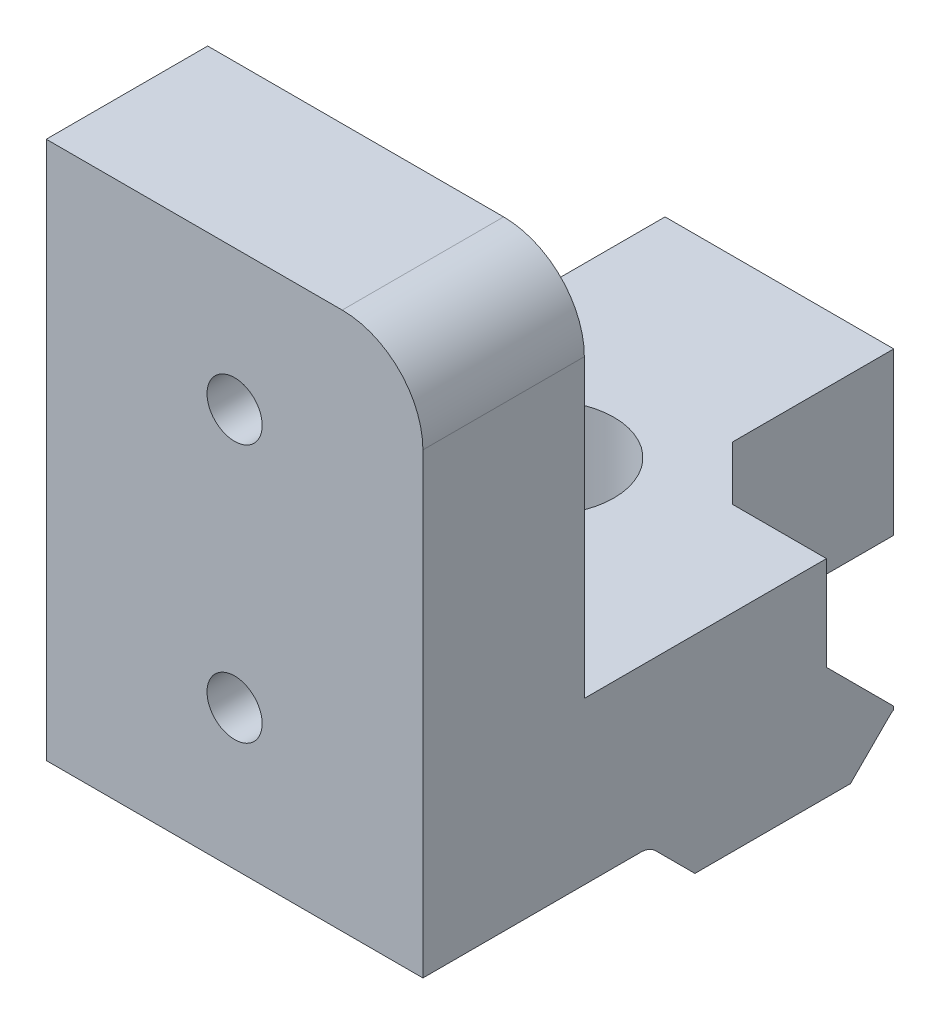
SolidWorks part; units mm, degrees
ref_plane "Front Plane" through (0, 0, 0) normal (0, 0, 1) x (1, 0, 0)
ref_plane "Top Plane" through (0, 0, 0) normal (0, 1, 0) x (1, 0, 0)
ref_plane "Right Plane" through (0, 0, 0) normal (1, 0, 0) x (0, 0, -1)
sketch "Sketch1" plane through (32.3643, 0, 0) normal (1, 0, 0) x (0, 0, -1)
  line L0 (-10.7659, 34.0751) -> (-4.9859, 34.0751)
  line L1 (-17.8759, 35.7651) -> (2.1241, 35.7651)
  line L2 (-17.8759, 35.7651) -> (-17.8759, 41.7651)
  line L3 (-17.8759, 41.7651) -> (2.1241, 41.7651)
  line L4 (2.1241, 35.7651) -> (2.1241, 41.7651)
  line L52 (-5.5365, 22.3651) -> (-2.3759, 19.2044)
  line L53 (-2.3759, 19.2044) -> (-2.3759, 17.5651)
  line L54 (-2.3759, 17.5651) -> (-4.9859, 17.5651)
  line L55 (-4.9859, 17.5651) -> (-4.9859, 17.4551)
  line L56 (-4.9859, 17.4551) -> (-3.5273, 15.9964)
  line L57 (-2.9686, 15.7651) -> (0.6241, 15.7651)
  line L58 (2.1241, 17.2651) -> (2.1241, 20.8578)
  line L59 (1.8927, 21.4164) -> (0.4341, 22.8751)
  line L60 (0.4341, 22.8751) -> (0.3241, 22.8751)
  line L61 (0.3241, 22.8751) -> (0.3241, 20.2651)
  line L62 (0.3241, 20.2651) -> (-1.3152, 20.2651)
  line L63 (-1.3152, 20.2651) -> (-4.4759, 23.4257)
  line L64 (-4.4759, 23.4257) -> (-4.4759, 28.1044)
  line L65 (-4.4759, 28.1044) -> (-1.3152, 31.2651)
  line L66 (-1.3152, 31.2651) -> (0.3241, 31.2651)
  line L67 (0.3241, 31.2651) -> (0.3241, 28.6551)
  line L68 (0.3241, 28.6551) -> (0.4341, 28.6551)
  line L69 (0.4341, 28.6551) -> (1.8927, 30.1137)
  line L70 (2.1241, 30.6723) -> (2.1241, 34.2651)
  line L71 (0.6241, 35.7651) -> (-2.9686, 35.7651)
  line L72 (-3.5273, 35.5337) -> (-4.9859, 34.0751)
  line L73 (-4.9859, 34.0751) -> (-4.9859, 33.9651)
  line L74 (-4.9859, 33.9651) -> (-2.3759, 33.9651)
  line L75 (-2.3759, 33.9651) -> (-2.3759, 32.3257)
  line L76 (-2.3759, 32.3257) -> (-5.5365, 29.1651)
  line L77 (-5.5365, 29.1651) -> (-10.2152, 29.1651)
  line L78 (-10.2152, 29.1651) -> (-13.3759, 32.3257)
  line L79 (-13.3759, 32.3257) -> (-13.3759, 33.9651)
  line L80 (-13.3759, 33.9651) -> (-10.7659, 33.9651)
  line L81 (-10.7659, 33.9651) -> (-10.7659, 34.0751)
  line L82 (-10.7659, 34.0751) -> (-12.2245, 35.5337)
  line L83 (-12.7831, 35.7651) -> (-16.3759, 35.7651)
  line L84 (-17.8759, 34.2651) -> (-17.8759, 30.6723)
  line L85 (-17.6445, 30.1137) -> (-16.1859, 28.6551)
  line L86 (-16.1859, 28.6551) -> (-16.0759, 28.6551)
  line L87 (-16.0759, 28.6551) -> (-16.0759, 31.2651)
  line L88 (-16.0759, 31.2651) -> (-14.4365, 31.2651)
  line L89 (-14.4365, 31.2651) -> (-11.2759, 28.1044)
  line L90 (-11.2759, 28.1044) -> (-11.2759, 23.4257)
  line L91 (-11.2759, 23.4257) -> (-14.4365, 20.2651)
  line L92 (-14.4365, 20.2651) -> (-16.0759, 20.2651)
  line L93 (-16.0759, 20.2651) -> (-16.0759, 22.8751)
  line L94 (-16.0759, 22.8751) -> (-16.1859, 22.8751)
  line L95 (-16.1859, 22.8751) -> (-17.6445, 21.4164)
  line L96 (-17.8759, 20.8578) -> (-17.8759, 17.2651)
  line L97 (-16.3759, 15.7651) -> (-12.7831, 15.7651)
  line L98 (-12.2245, 15.9964) -> (-10.7659, 17.4551)
  line L99 (-10.7659, 17.4551) -> (-10.7659, 17.5651)
  line L100 (-10.7659, 17.5651) -> (-13.3759, 17.5651)
  line L101 (-13.3759, 17.5651) -> (-13.3759, 19.2044)
  line L102 (-13.3759, 19.2044) -> (-10.2152, 22.3651)
  line L103 (-10.2152, 22.3651) -> (-5.5365, 22.3651)
  line L104 (-5.5365, 22.3651) -> (-2.3759, 19.2044)
  line L105 (-2.3759, 19.2044) -> (-2.3759, 17.5651)
  line L106 (-2.3759, 17.5651) -> (-4.9859, 17.5651)
  line L107 (-4.9859, 17.5651) -> (-4.9859, 17.4551)
  line L108 (-4.9859, 17.4551) -> (-3.5273, 15.9964)
  line L109 (-2.9686, 15.7651) -> (0.6241, 15.7651)
  line L110 (2.1241, 17.2651) -> (2.1241, 20.8578)
  line L111 (1.8927, 21.4164) -> (0.4341, 22.8751)
  line L112 (0.4341, 22.8751) -> (0.3241, 22.8751)
  line L113 (0.3241, 22.8751) -> (0.3241, 20.2651)
  line L114 (0.3241, 20.2651) -> (-1.3152, 20.2651)
  line L115 (-1.3152, 20.2651) -> (-4.4759, 23.4257)
  line L116 (-4.4759, 23.4257) -> (-4.4759, 28.1044)
  line L117 (-4.4759, 28.1044) -> (-1.3152, 31.2651)
  line L118 (-1.3152, 31.2651) -> (0.3241, 31.2651)
  line L119 (0.3241, 31.2651) -> (0.3241, 28.6551)
  line L120 (0.3241, 28.6551) -> (0.4341, 28.6551)
  line L121 (0.4341, 28.6551) -> (1.8927, 30.1137)
  line L122 (2.1241, 30.6723) -> (2.1241, 34.2651)
  line L123 (0.6241, 35.7651) -> (-2.9686, 35.7651)
  line L124 (-3.5273, 35.5337) -> (-4.9859, 34.0751)
  line L125 (-4.9859, 34.0751) -> (-4.9859, 33.9651)
  line L126 (-4.9859, 33.9651) -> (-2.3759, 33.9651)
  line L127 (-2.3759, 33.9651) -> (-2.3759, 32.3257)
  line L128 (-2.3759, 32.3257) -> (-5.5365, 29.1651)
  line L129 (-5.5365, 29.1651) -> (-10.2152, 29.1651)
  line L130 (-10.2152, 29.1651) -> (-13.3759, 32.3257)
  line L131 (-13.3759, 32.3257) -> (-13.3759, 33.9651)
  line L132 (-13.3759, 33.9651) -> (-10.7659, 33.9651)
  line L133 (-10.7659, 33.9651) -> (-10.7659, 34.0751)
  line L134 (-10.7659, 34.0751) -> (-12.2245, 35.5337)
  line L135 (-12.7831, 35.7651) -> (-16.3759, 35.7651)
  line L136 (-17.8759, 34.2651) -> (-17.8759, 30.6723)
  line L137 (-17.6445, 30.1137) -> (-16.1859, 28.6551)
  line L138 (-16.1859, 28.6551) -> (-16.0759, 28.6551)
  line L139 (-16.0759, 28.6551) -> (-16.0759, 31.2651)
  line L140 (-16.0759, 31.2651) -> (-14.4365, 31.2651)
  line L141 (-14.4365, 31.2651) -> (-11.2759, 28.1044)
  line L142 (-11.2759, 28.1044) -> (-11.2759, 23.4257)
  line L143 (-11.2759, 23.4257) -> (-14.4365, 20.2651)
  line L144 (-14.4365, 20.2651) -> (-16.0759, 20.2651)
  line L145 (-16.0759, 20.2651) -> (-16.0759, 22.8751)
  line L146 (-16.0759, 22.8751) -> (-16.1859, 22.8751)
  line L147 (-16.1859, 22.8751) -> (-17.6445, 21.4164)
  line L148 (-17.8759, 20.8578) -> (-17.8759, 17.2651)
  line L149 (-16.3759, 15.7651) -> (-12.7831, 15.7651)
  line L150 (-12.2245, 15.9964) -> (-10.7659, 17.4551)
  line L151 (-10.7659, 17.4551) -> (-10.7659, 17.5651)
  line L152 (-10.7659, 17.5651) -> (-13.3759, 17.5651)
  line L153 (-13.3759, 17.5651) -> (-13.3759, 19.2044)
  line L154 (-13.3759, 19.2044) -> (-10.2152, 22.3651)
  line L155 (-10.2152, 22.3651) -> (-5.5365, 22.3651)
  arc A12 (-3.5273, 15.9964) -> (-2.9686, 15.7651) centre (-2.9686, 16.5551) ccw
  arc A13 (0.6241, 15.7651) -> (2.1241, 17.2651) centre (0.6241, 17.2651) ccw
  arc A14 (2.1241, 20.8578) -> (1.8927, 21.4164) centre (1.3341, 20.8578) ccw
  arc A15 (1.8927, 30.1137) -> (2.1241, 30.6723) centre (1.3341, 30.6723) ccw
  arc A16 (2.1241, 34.2651) -> (0.6241, 35.7651) centre (0.6241, 34.2651) ccw
  arc A17 (-2.9686, 35.7651) -> (-3.5273, 35.5337) centre (-2.9686, 34.9751) ccw
  arc A18 (-12.2245, 35.5337) -> (-12.7831, 35.7651) centre (-12.7831, 34.9751) ccw
  arc A19 (-16.3759, 35.7651) -> (-17.8759, 34.2651) centre (-16.3759, 34.2651) ccw
  arc A20 (-17.8759, 30.6723) -> (-17.6445, 30.1137) centre (-17.0859, 30.6723) ccw
  arc A21 (-17.6445, 21.4164) -> (-17.8759, 20.8578) centre (-17.0859, 20.8578) ccw
  arc A22 (-17.8759, 17.2651) -> (-16.3759, 15.7651) centre (-16.3759, 17.2651) ccw
  arc A23 (-12.7831, 15.7651) -> (-12.2245, 15.9964) centre (-12.7831, 16.5551) ccw
  arc A24 (-3.5273, 15.9964) -> (-2.9686, 15.7651) centre (-2.9686, 16.5551) ccw
  arc A25 (0.6241, 15.7651) -> (2.1241, 17.2651) centre (0.6241, 17.2651) ccw
  arc A26 (2.1241, 20.8578) -> (1.8927, 21.4164) centre (1.3341, 20.8578) ccw
  arc A27 (1.8927, 30.1137) -> (2.1241, 30.6723) centre (1.3341, 30.6723) ccw
  arc A28 (2.1241, 34.2651) -> (0.6241, 35.7651) centre (0.6241, 34.2651) ccw
  arc A29 (-2.9686, 35.7651) -> (-3.5273, 35.5337) centre (-2.9686, 34.9751) ccw
  arc A30 (-12.2245, 35.5337) -> (-12.7831, 35.7651) centre (-12.7831, 34.9751) ccw
  arc A31 (-16.3759, 35.7651) -> (-17.8759, 34.2651) centre (-16.3759, 34.2651) ccw
  arc A32 (-17.8759, 30.6723) -> (-17.6445, 30.1137) centre (-17.0859, 30.6723) ccw
  arc A33 (-17.6445, 21.4164) -> (-17.8759, 20.8578) centre (-17.0859, 20.8578) ccw
  arc A34 (-17.8759, 17.2651) -> (-16.3759, 15.7651) centre (-16.3759, 17.2651) ccw
  arc A35 (-12.7831, 15.7651) -> (-12.2245, 15.9964) centre (-12.7831, 16.5551) ccw
  dimension "D2" = 6
  dimension "D1" = 0
extrude "Boss-Extrude1" add sketch "Sketch1" along normal blind 14 contours L1 L4 L3 L2 | A30 L134 L0 L124 A29 L1
sketch "Sketch2" plane through (0, 34.0751, 0) normal (0, -1, 0) x (1, 0, 0)
  line L0 (46.3643, 7.8759) -> (32.3643, 7.8759) construction
  line L1 (32.3643, 10.7659) -> (32.3643, 4.9859) construction
  line L2 (46.3643, 10.7659) -> (46.3643, 4.9859) construction
  circle A0 centre (37.8643, 7.8759) radius 2.6
  dimension "D1" = 5.2
  dimension "D2" = 5.5
extrude "Cut-Extrude1" cut sketch "Sketch2" against normal up to next
sketch "Sketch3" plane through (0, 0, 17.8759) normal (0, 0, 1) x (1, 0, 0)
  line L1 (32.3643, 35.7651) -> (46.3643, 35.7651)
  line L2 (32.3643, 35.7651) -> (32.3643, 55.7651)
  line L3 (32.3643, 55.7651) -> (46.3643, 55.7651)
  line L4 (46.3643, 35.7651) -> (46.3643, 55.7651)
  line L6 (46.3643, 35.7651) -> (46.3643, 41.7651) construction
  dimension "D1" = 20
extrude "Boss-Extrude2" add sketch "Sketch3" along normal blind 3 and the other way blind 3
sketch "Sketch4" plane through (0, 0, 20.8759) normal (0, 0, 1) x (1, 0, 0)
  line L0 (32.3643, 55.7651) -> (32.3643, 35.7651) construction
  line L1 (32.3643, 35.7651) -> (46.3643, 35.7651) construction
  circle A0 centre (39.3643, 50.5651) radius 1.025
  circle A1 centre (39.3643, 40.9651) radius 1.025
  dimension "D1" = 7
  dimension "D5" = 2.05
  dimension "D6" = 2.05
  dimension "D2" = 7
  dimension "D3" = 9.6
  dimension "D4" = 5.2
extrude "Cut-Extrude4" cut sketch "Sketch4" against normal blind 6
sketch "Sketch5" plane through (0, 41.7651, 0) normal (0, 1, 0) x (1, 0, 0)
  line L1 (40.8643, -5.8759) -> (46.3643, -5.8759)
  line L2 (40.8643, -5.8759) -> (40.8643, 2.1241)
  line L3 (40.8643, 2.1241) -> (46.3643, 2.1241)
  line L4 (46.3643, -5.8759) -> (46.3643, 2.1241)
  dimension "D1" = 5.5
  dimension "D2" = 8
extrude "Cut-Extrude5" cut sketch "Sketch5" against normal up to surface (6 mm away) up to face at (39.3643, 35.7651, 0.4223)
chamfer "Chamfer1" distance 2 angle 45 1 edges at (40.8643, 38.7651, 5.8759)
chamfer "Chamfer2" distance 2.5 angle 45 1 edges at (44.6143, 35.7651, 5.8759)
sketch "Sketch6" plane through (0, 35.7651, 0) normal (0, 1, 0) x (1, 0, 0)
  line L4 (40.8643, -2.9686) -> (40.8643, -3.3759)
  line L5 (40.8643, -3.3759) -> (46.3643, -3.3759)
  line L6 (46.3643, -3.3759) -> (46.3643, -2.9686)
  line L7 (46.3643, -2.9686) -> (40.8643, -2.9686)
  line L8 (40.8643, -2.9686) -> (40.8643, -3.3759)
  line L9 (40.8643, -3.3759) -> (46.3643, -3.3759)
  line L10 (46.3643, -3.3759) -> (46.3643, -2.9686)
  line L11 (46.3643, -2.9686) -> (40.8643, -2.9686)
  dimension "D1" = 0
extrude "Cut-Extrude6" cut sketch "Sketch6" against normal through all
fillet "Fillet1" radius 3 1 edges at (46.3643, 55.7651, 17.8759)
